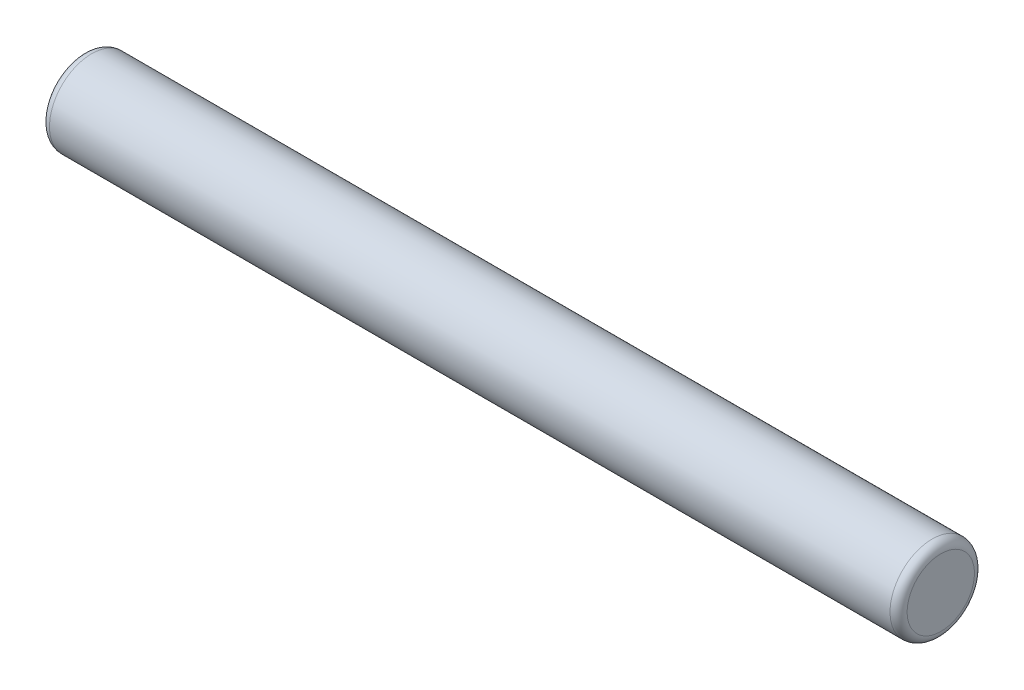
SolidWorks part; units mm, degrees
ref_plane "Front Plane" through (0, 0, 0) normal (0, 0, 1) x (1, 0, 0)
ref_plane "Top Plane" through (0, 0, 0) normal (0, 1, 0) x (1, 0, 0)
ref_plane "Right Plane" through (0, 0, 0) normal (1, 0, 0) x (0, 0, -1)
sketch "Sketch1" plane through (0, 0, 0) normal (1, 0, 0) x (0, 0, -1)
  circle A0 centre (0, 0) radius 2.5
  dimension "D1" = 5
extrude "Boss-Extrude1" add sketch "Sketch1" along normal blind 50.8
fillet "Fillet1" radius 0.508 2 edges at (50.8, 0, -2.5) (0, 0, -2.5)
